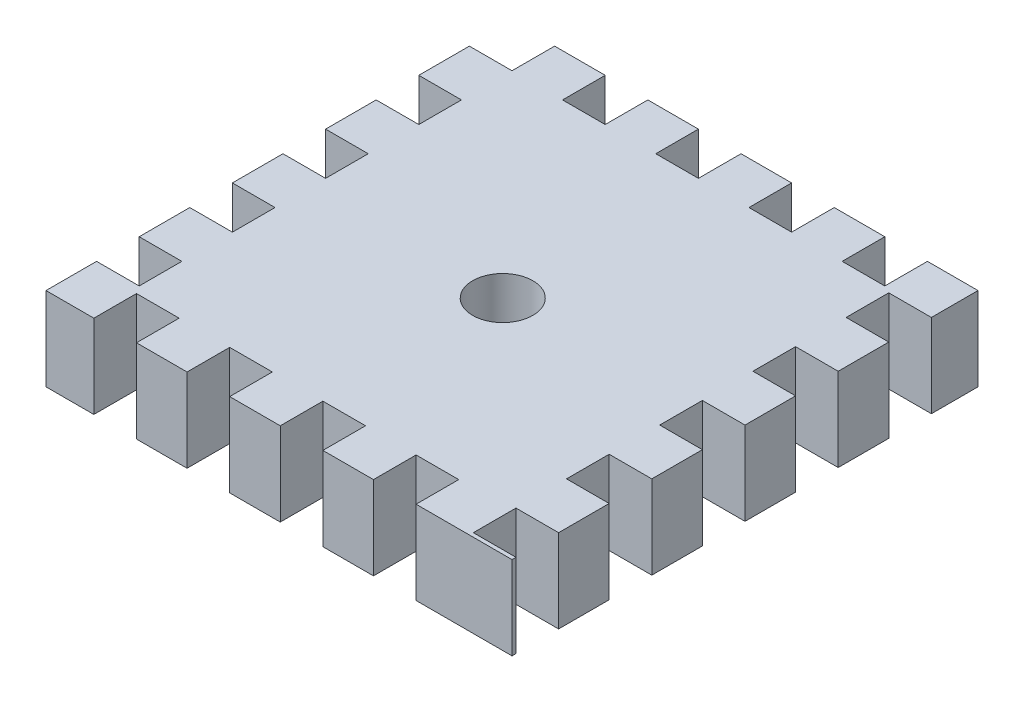
SolidWorks part; units mm, degrees
ref_plane "Front Plane" through (0, 0, 0) normal (0, 0, 1) x (1, 0, 0)
ref_plane "Top Plane" through (0, 0, 0) normal (0, 1, 0) x (1, 0, 0)
ref_plane "Right Plane" through (0, 0, 0) normal (1, 0, 0) x (0, 0, -1)
sketch "Sketch3" plane through (0, 0, 0) normal (0, 1, 0) x (1, 0, 0)
  line L9 (20.6915, -51.1944) -> (71.4915, -51.1944)
  line L10 (20.6915, -51.1944) -> (20.6915, -101.9944)
  line L11 (20.6915, -101.9944) -> (71.4915, -101.9944)
  line L12 (71.4915, -51.1944) -> (71.4915, -101.9944)
  line L17 (20.6915, -51.1944) -> (23.0006, -51.1944)
  line L18 (20.6915, -51.1944) -> (20.6915, -53.5035)
  line L19 (20.6915, -53.5035) -> (23.0006, -53.5035)
  line L20 (23.0006, -51.1944) -> (23.0006, -53.5035)
extrude "Boss-Extrude5" add sketch "Sketch3" along normal blind 4.572 and the other way blind 4.5212
sketch "Sketch4" plane through (0, 4.572, 0) normal (0, 1, 0) x (1, 0, 0)
  line L1 (20.6915, -51.1944) -> (25.3397, -51.1944)
  line L2 (20.6915, -51.1944) -> (20.6915, -55.8426)
  line L3 (20.6915, -55.8426) -> (25.3397, -55.8426)
  line L4 (25.3397, -51.1944) -> (25.3397, -55.8426)
  point P5 (0, 0)
extrude "Cut-Extrude4" cut sketch "Sketch4" against normal up to vertex (9.0932 mm away)
sketch "Sketch9" plane through (0, 4.572, 0) normal (0, 1, 0) x (1, 0, 0)
  line L0 (25.3397, -55.8426) -> (25.3397, -51.1944) construction
  line L5 (71.4915, -56.2744) -> (66.8433, -56.2744)
  line L6 (71.4915, -56.2744) -> (71.4915, -60.9226)
  line L7 (71.4915, -60.9226) -> (66.8433, -60.9226)
  line L8 (66.8433, -56.2744) -> (66.8433, -60.9226)
  point P1 (0, 0)
  point P2 (0, 0)
  point P3 (0, 0)
  point P8 (0, 0)
  point P10 (0, 0)
  point P11 (0, 0)
  point P12 (0, 0)
  point P13 (0, 0)
  point P15 (0, 0)
sketch "Sketch10" plane through (0, 4.572, 0) normal (0, 1, 0) x (1, 0, 0)
  circle A0 centre (46.2972, -77.81) radius 3.2807
extrude "Cut-Extrude9" cut sketch "Sketch10" against normal blind 5.08
extrude "Cut-Extrude10" cut sketch "Sketch9" against normal blind 9.144
pattern_linear "LPattern1" count 5 spacing 10.16 along (0, 0, 1) of "Cut-Extrude4"
pattern_linear "LPattern2" count 5 spacing 10.16 along (0, 0, 1) of "Cut-Extrude10"
pattern_linear "LPattern3" count 5 spacing 10.16 along (1, 0, 0) of "Cut-Extrude4"
sketch "Sketch13" plane through (0, 4.572, 0) normal (0, 1, 0) x (1, 0, 0)
  line L0 (51.1715, -55.8426) -> (55.8197, -55.8426) construction
  line L1 (25.908, -97.3462) -> (30.5562, -97.3462)
  line L2 (25.908, -97.3462) -> (25.908, -101.9944)
  line L3 (25.908, -101.9944) -> (30.5562, -101.9944)
  line L4 (30.5562, -97.3462) -> (30.5562, -101.9944)
  line L6 (20.6915, -101.9944) -> (71.4915, -101.9944) construction
  point P4 (0, 0)
  point P5 (0, 0)
  point P6 (0, 0)
  point P7 (0, 0)
  point P9 (0, 0)
  point P11 (0, 0)
  point P12 (0, 0)
  point P14 (0, 0)
  point P15 (0, 0)
  point P16 (0, 0)
  point P18 (0, 0)
  point P19 (0, 0)
  point P21 (0, 0)
  point P22 (0, 0)
  point P23 (0, 0)
  point P24 (0, 0)
  point P27 (0, 0)
  point P28 (0, 0)
  point P31 (0, 0)
extrude "Cut-Extrude11" cut sketch "Sketch13" against normal blind 9.144
pattern_linear "LPattern4" count 4 spacing 10.16 along (1, 0, 0) of "Cut-Extrude11"
equation "\"square_width\" = \"desired_width\" - \"laser_width\""
equation "\"num_squares\"= 1 / \"desired_width\""
equation "\"square_width@Sketch4\"= \"square_width\""
equation "\"hole_width\"= \"desired_width\" + \"laser_width\""
equation "\"desired_width\"= 1 / 5"
equation "\"laser_width\"= 0.017"
